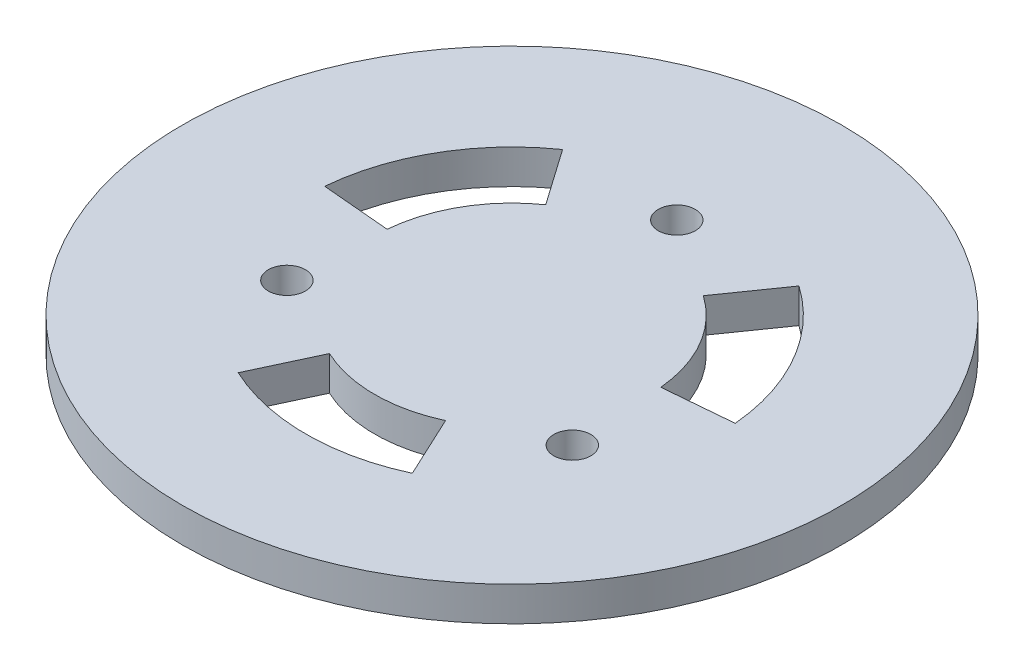
SolidWorks part; units mm, degrees
ref_plane "Front Plane" through (0, 0, 0) normal (0, 0, 1) x (1, 0, 0)
ref_plane "Top Plane" through (0, 0, 0) normal (0, 1, 0) x (1, 0, 0)
ref_plane "Right Plane" through (0, 0, 0) normal (1, 0, 0) x (0, 0, -1)
sketch "Sketch1" plane through (0, 0, 0) normal (0, 1, 0) x (1, 0, 0)
  line L0 (0, 0) -> (0, 23.9927) construction
  circle A0 centre (0, 0) radius 23.9927
  circle A1 centre (0, 11.9963) radius 1.35
  circle A2 centre (10.3891, -5.9982) radius 1.35
  circle A3 centre (-10.3891, -5.9982) radius 1.35
  point P13 (0, 0)
  dimension "D1" = 47.9854
  dimension "D2" = 2.7
  dimension "D4" = 11.9963
  dimension "D3" = 3
extrude "Boss-Extrude1" add sketch "Sketch1" along normal blind 2.5
sketch "Sketch3" plane through (0, 2.5, 0) normal (0, 1, 0) x (1, 0, 0)
  line L0 (5.7358, 8.1915) -> (8.6036, 12.2873)
  line L1 (0, 0) -> (28.6334, 16.5315) construction
  line L2 (0, 0) -> (0, 25.5344) construction
  line L3 (9.9619, 0.8716) -> (14.9429, 1.3073)
  line L4 (4.2262, -9.0631) -> (6.3393, -13.5946)
  line L5 (-4.2262, -9.0631) -> (-6.3393, -13.5946)
  line L6 (-9.9619, 0.8716) -> (-14.9429, 1.3073)
  line L7 (-5.7358, 8.1915) -> (-8.6036, 12.2873)
  arc A0 (9.9619, 0.8716) -> (5.7358, 8.1915) centre (0, 0) ccw
  arc A1 (14.9429, 1.3073) -> (8.6036, 12.2873) centre (0, 0) ccw
  arc A2 (-6.3393, -13.5946) -> (6.3393, -13.5946) centre (0, 0) ccw
  arc A3 (-4.2262, -9.0631) -> (4.2262, -9.0631) centre (0, 0) ccw
  arc A4 (-8.6036, 12.2873) -> (-14.9429, 1.3073) centre (0, 0) ccw
  arc A5 (-5.7358, 8.1915) -> (-9.9619, 0.8716) centre (0, 0) ccw
  point P19 (0, 0)
  dimension "D1" = 30
  dimension "D2" = 20
  dimension "D3" = 60
  dimension "D4" = 25
extrude "Cut-Extrude2" cut sketch "Sketch3" against normal blind 10
